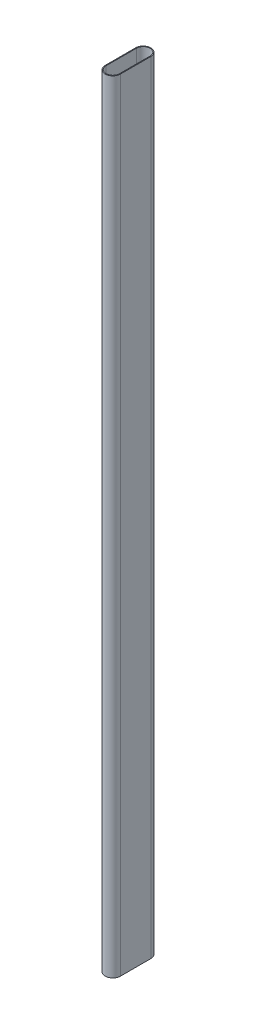
SolidWorks part; units mm, degrees
material "Beryllium Copper, UNS C17000"
ref_plane "Front Plane" through (0, 0, 0) normal (0, 0, 1) x (1, 0, 0)
ref_plane "Top Plane" through (0, 0, 0) normal (0, 1, 0) x (1, 0, 0)
ref_plane "Right Plane" through (0, 0, 0) normal (1, 0, 0) x (0, 0, -1)
sketch "Sketch1" plane through (0, 0, 0) normal (0, 1, 0) x (1, 0, 0)
  line L0 (0, -10) -> (0, 10) construction
  line L1 (-5, -10) -> (-5, 10)
  line L2 (5, -10) -> (5, 10)
  arc A0 (-5, -10) -> (5, -10) centre (0, -10) ccw
  arc A1 (5, 10) -> (-5, 10) centre (0, 10) ccw
  point P3 (0, 0)
  dimension "D1" = 5
  dimension "D2" = 20
extrude "Extrude-Thin1" add sketch "Sketch1" along normal blind 515 thin
